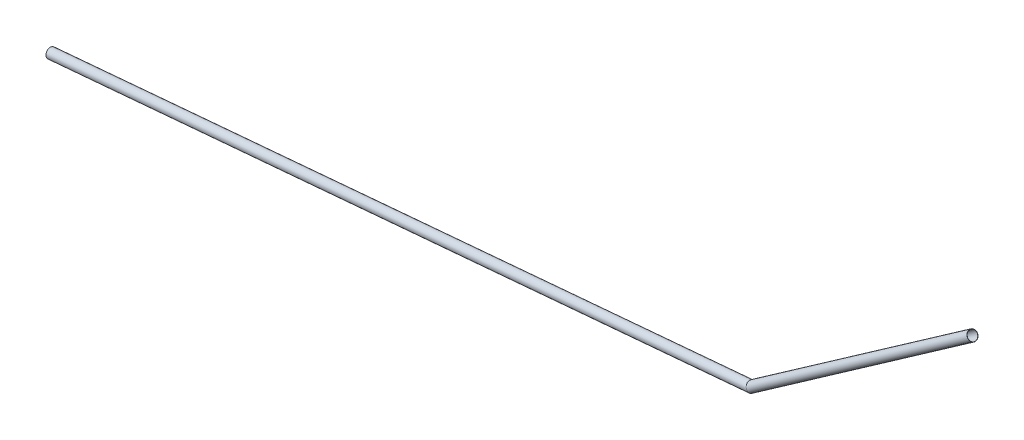
SolidWorks part; units mm, degrees
ref_plane "Front Plane" through (0, 0, 0) normal (0, 0, 1) x (1, 0, 0)
ref_plane "Top Plane" through (0, 0, 0) normal (0, 1, 0) x (1, 0, 0)
ref_plane "Right Plane" through (0, 0, 0) normal (1, 0, 0) x (0, 0, -1)
sketch "Sketch1" plane through (0, 0, 0) normal (1, 0, 0) x (0, 0, -1)
  line L0 (-8.4165, 0) -> (8.3779, 0) construction
sketch "Sketch2" plane through (0, 0, 0) normal (0, 0, 1) x (1, 0, 0)
  line L0 (-23.5253, 0) -> (23.5253, 0) construction
  line L1 (0, 0) -> (380, 33.2457)
  line L2 (380, 33.2457) -> (500, 117.2706)
  line L3 (380, 33.2457) -> (73.2093, 6.405) construction
  dimension "D1" = 5
  dimension "D2" = 30
  dimension "D3" = 500
  dimension "D4" = 380
ref_plane "Plane1" through (0, 0, 0) normal (0.9962, 0.0872, 0) x (0, 0, -1)
sketch "Sketch3" plane through (0, 0, 0) normal (0.9962, 0.0872, 0) x (0, 0, -1)
  circle A0 centre (0, 0) radius 2.5
  dimension "D1" = 5
sweep "Sweep-Thin1" add profiles "Sketch3" path "Sketch2" parameters "D1"=0.1
